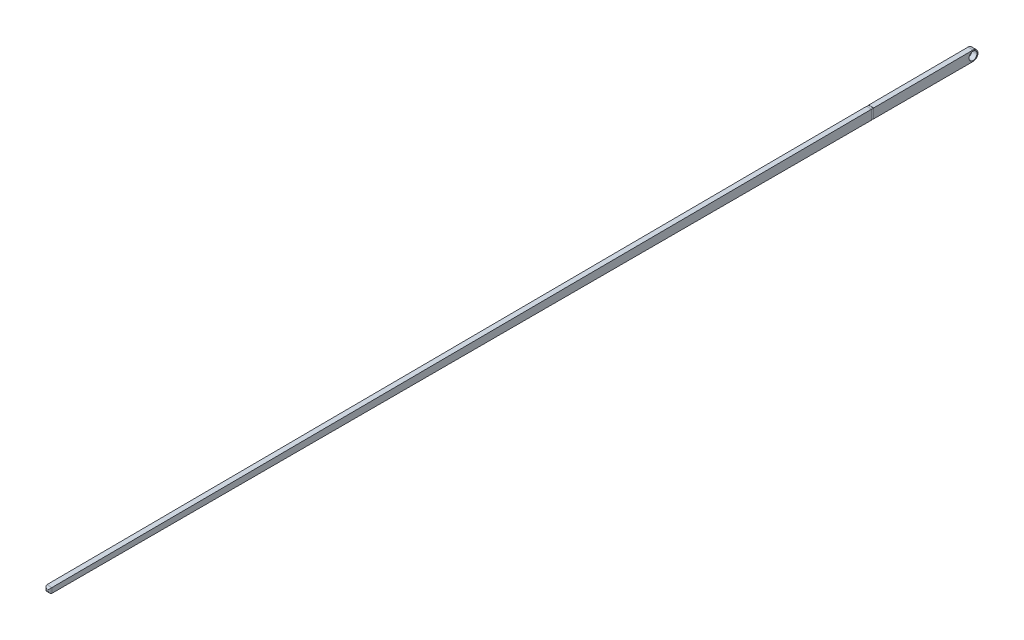
SolidWorks part; units mm, degrees
ref_plane "Front Plane" through (0, 0, 0) normal (0, 0, 1) x (1, 0, 0)
ref_plane "Top Plane" through (0, 0, 0) normal (0, 1, 0) x (1, 0, 0)
ref_plane "Right Plane" through (0, 0, 0) normal (1, 0, 0) x (0, 0, -1)
sketch "Sketch2" plane through (0, 0, 0) normal (1, 0, 0) x (0, 0, -1)
  line L0 (0, -0.635) -> (-116.84, -0.635)
  line L1 (-0.0035, 0.635) -> (-116.84, 0)
  line L2 (-116.84, 0) -> (-116.84, -0.635)
  arc A0 (-0.0035, 0.635) -> (0, -0.635) centre (0, 0) cw
  circle A1 centre (0, 0) radius 0.508
  dimension "D1" = 0.635
  dimension "D2" = 1.016
  dimension "D3" = 0.635
  dimension "D4" = 116.84
extrude "Boss-Extrude1" add sketch "Sketch2" along normal mid plane 0.635
fillet "Fillet1" radius 0.254 4 edges at (0, 0, 116.84) (0.3175, -0.3175, 116.84) (0, -0.635, 116.84) (-0.3175, -0.3175, 116.84)
ref_plane "Plane1" through (0, 0, 12.7) normal (0, 0, 1) x (1, 0, 0)
sketch "Sketch3" plane through (0, 0, 12.7) normal (0, 0, 1) x (1, 0, 0)
  line L1 (-0.3175, 0.566) -> (0.3175, 0.566) construction
  line L2 (-0.3175, 0.566) -> (-0.3175, -0.635) construction
  line L3 (-0.3175, -0.635) -> (0.3175, -0.635) construction
  line L4 (0.3175, 0.566) -> (0.3175, -0.635) construction
  line L5 (-0.3175, 0.566) -> (0.3175, -0.635) construction
  line L6 (-0.3175, -0.635) -> (0.3175, 0.566) construction
  line L11 (-0.3048, -0.6096) -> (0.3048, -0.6096)
  line L12 (-0.3048, -0.6096) -> (-0.3048, 0.5406)
  line L13 (-0.3048, 0.5406) -> (0.3048, 0.5406)
  line L14 (0.3048, -0.6096) -> (0.3048, 0.5406)
  line L15 (-0.3048, -0.6096) -> (0.3048, 0.5406) construction
  line L16 (-0.3048, 0.5406) -> (0.3048, -0.6096) construction
  line L17 (-0.508, -0.7965) -> (0.508, -0.7965)
  line L18 (-0.508, -0.7965) -> (-0.508, 0.7275)
  line L19 (-0.508, 0.7275) -> (0.508, 0.7275)
  line L20 (0.508, -0.7965) -> (0.508, 0.7275)
  line L21 (-0.508, -0.7965) -> (0.508, 0.7275) construction
  line L22 (-0.508, 0.7275) -> (0.508, -0.7965) construction
  point P0 (0, -0.0345)
  point P5 (0, -0.0345)
  point P12 (0, -0.0345)
  dimension "D1" = 0.0254
  dimension "D2" = 0.0254
  dimension "D3" = 1.524
  dimension "D4" = 1.016
extrude "Cut-Extrude1" cut sketch "Sketch3" against normal mid plane 0.254
